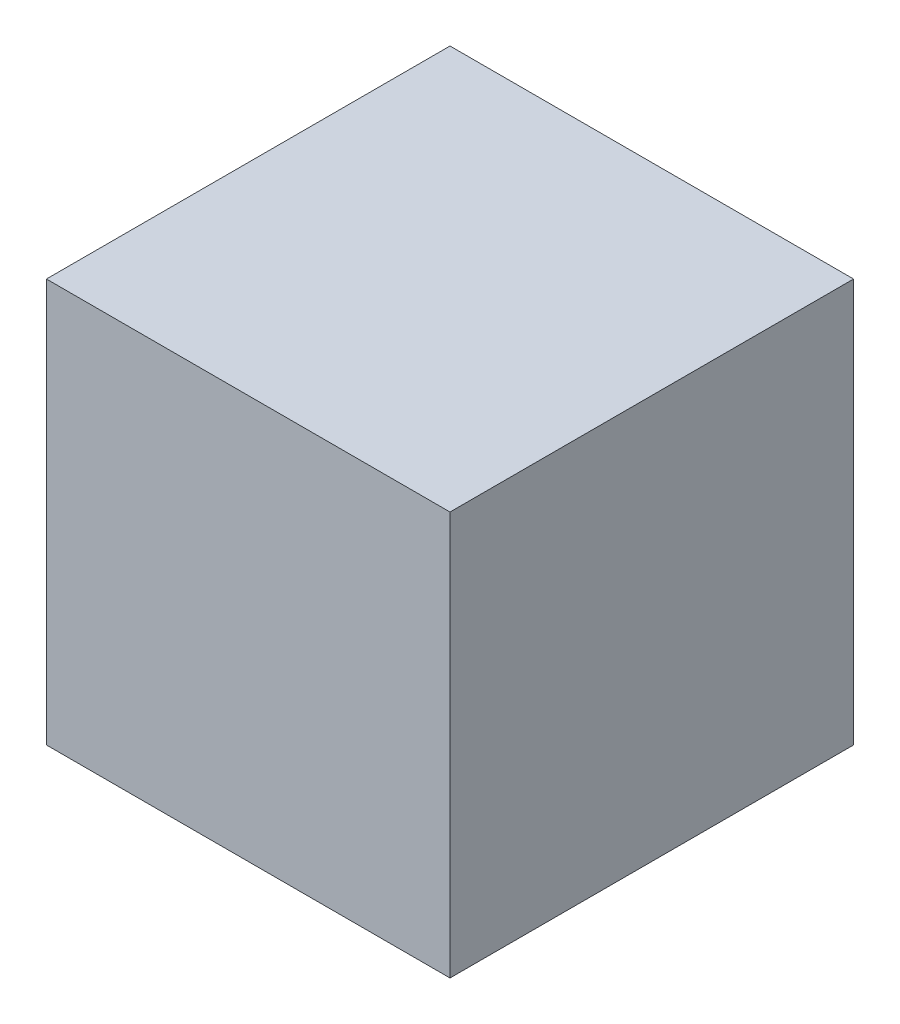
SolidWorks part; units mm, degrees
ref_plane "Front Plane" through (0, 0, 0) normal (0, 0, 1) x (1, 0, 0)
ref_plane "Top Plane" through (0, 0, 0) normal (0, 1, 0) x (1, 0, 0)
ref_plane "Right Plane" through (0, 0, 0) normal (1, 0, 0) x (0, 0, -1)
sketch "Sketch2" plane through (0, 0, 0) normal (0, 1, 0) x (1, 0, 0)
  line L1 (0, 0) -> (1000, 0)
  line L2 (0, 0) -> (0, 1000)
  line L3 (0, 1000) -> (1000, 1000)
  line L4 (1000, 0) -> (1000, 1000)
  dimension "D1" = 1000
  dimension "D2" = 1000
extrude "Boss-Extrude1" add sketch "Sketch2" along normal blind 990
shell "Shell2" thickness 10
sketch "Sketch3" plane through (0, 990, 0) normal (0, 1, 0) x (1, 0, 0)
  line L1 (0, 1000) -> (1000, 1000)
  line L2 (0, 1000) -> (0, 0)
  line L3 (0, 0) -> (1000, 0)
  line L4 (1000, 1000) -> (1000, 0)
extrude "Boss-Extrude2" add sketch "Sketch3" along normal blind 10
